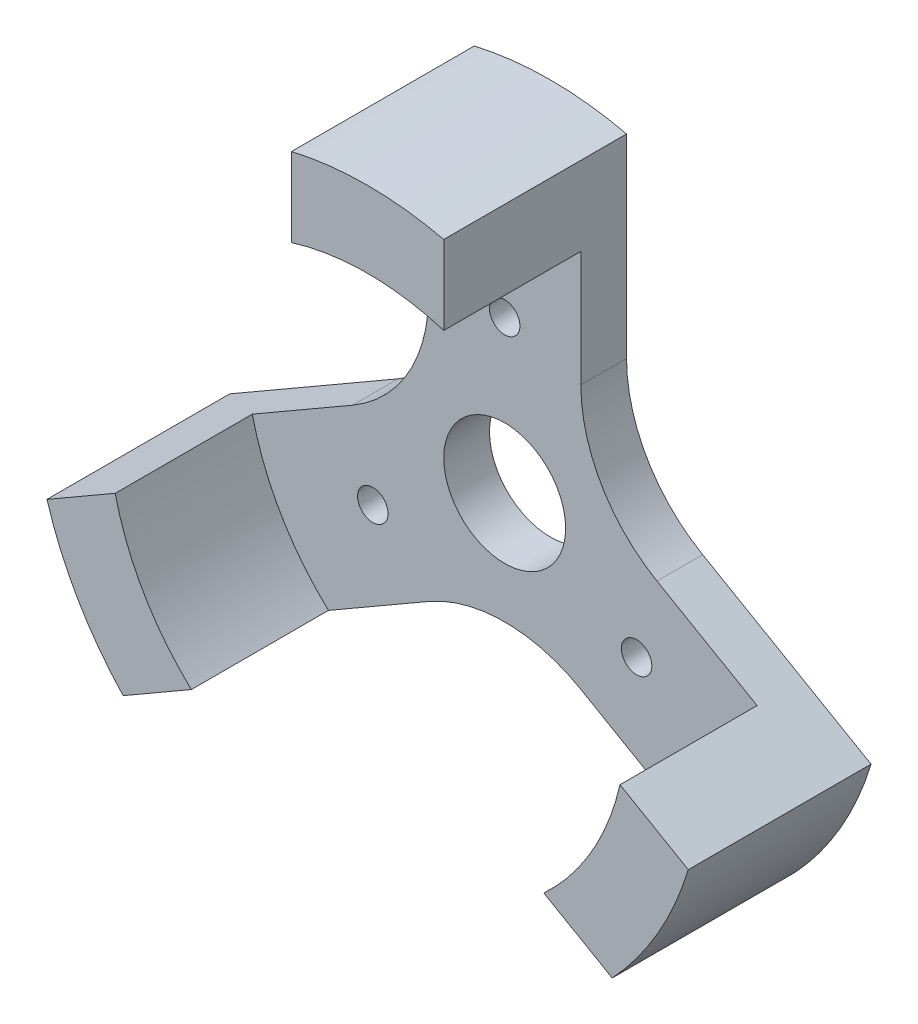
SolidWorks part; units mm, degrees
ref_plane "前视基准面" through (0, 0, 0) normal (0, 0, 1) x (1, 0, 0)
ref_plane "上视基准面" through (0, 0, 0) normal (0, 1, 0) x (1, 0, 0)
ref_plane "右视基准面" through (0, 0, 0) normal (1, 0, 0) x (0, 0, -1)
sketch "草图1" plane through (0, 0, 0) normal (0, 0, 1) x (1, 0, 0)
  circle A0 centre (0, 0) radius 22
  circle A1 centre (0, 0) radius 17
extrude "凸台-拉伸1" add sketch "草图1" along normal blind 9
sketch "草图2" plane through (0, 0, 0) normal (0, 0, -1) x (-1, 0, 0)
  circle A0 centre (0, 0) radius 22
extrude "凸台-拉伸2" add sketch "草图2" along normal blind 3
sketch "草图3" plane through (0, 0, -3) normal (0, 0, -1) x (-1, 0, 0)
  circle A1 centre (0, 10) radius 1
  circle A2 centre (8.6603, -5) radius 1
  circle A3 centre (-8.6603, -5) radius 1
  point P12 (0, 0)
  dimension "D1" = 3
extrude "切除-拉伸1" cut sketch "草图3" against normal blind 3
sketch "草图4" plane through (0, 0, -3) normal (0, 0, -1) x (-1, 0, 0)
  line L1 (24.7877, -8.5377) -> (5, 2.8868)
  line L2 (5, 15) -> (5, 2.8868)
  line L3 (-6.1603, -9.3301) -> (0, -5.7735)
  line L4 (19.7877, -17.1979) -> (0, -5.7735)
  line L5 (-5, 10) -> (-5, 2.8868)
  line L9 (-5, 2.8868) -> (-28.9027, -10.9135)
  line L16 (-6.1603, -9.3301) -> (-23.9027, -19.5738)
  line L19 (-5, 10) -> (-5, 31.0066)
  line L21 (5, 31.0066) -> (5, 15)
  line L22 (5, 31.0066) -> (28.5963, 19.5438)
  line L23 (28.5963, 19.5438) -> (24.7877, -8.5377)
  line L24 (19.7877, -17.1979) -> (-4.0351, -32.4361)
  line L25 (-4.0351, -32.4361) -> (-23.9027, -19.5738)
  line L26 (-28.9027, -10.9135) -> (-27.6381, 27.1706)
  line L27 (-27.6381, 27.1706) -> (-5, 31.0066)
extrude "切除-拉伸2" cut sketch "草图4" against normal blind 25
sketch "草图5" plane through (0, 0, -3) normal (0, 0, -1) x (-1, 0, 0)
  circle A0 centre (0, 0) radius 4
extrude "切除-拉伸3" cut sketch "草图5" against normal blind 10
fillet "圆角1" radius 10 1 edges at (-5, 2.8868, -1.5)
fillet "圆角2" radius 10 2 edges at (5, 2.8868, -1.5) (0, -5.7735, -1.5)
